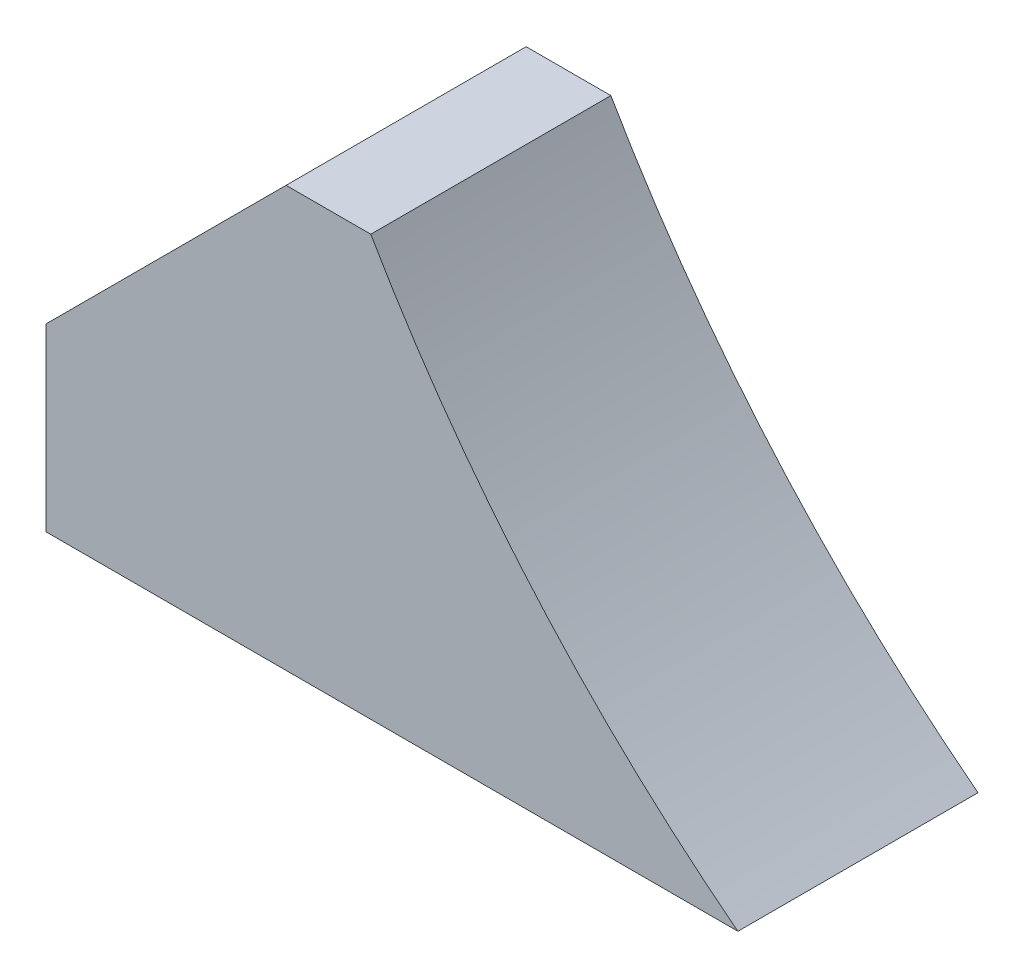
SolidWorks part; units mm, degrees
ref_plane "Front Plane" through (0, 0, 0) normal (0, 0, 1) x (1, 0, 0)
ref_plane "Top Plane" through (0, 0, 0) normal (0, 1, 0) x (1, 0, 0)
ref_plane "Right Plane" through (0, 0, 0) normal (1, 0, 0) x (0, 0, -1)
sketch "Sketch2" plane through (0, 0, 0) normal (0, 0, 1) x (1, 0, 0)
  line L0 (-28.3947, 6.35) -> (-101.6, 6.35)
  line L1 (-101.6, 6.35) -> (-101.6, 50.8)
  line L2 (-101.6, 50.8) -> (-67.2396, 50.8)
  line L3 (-67.2396, 50.8) -> (-101.6, 50.8) construction
  line L4 (-28.3666, 6.35) -> (-67.2396, 6.35) construction
  line L5 (-101.6, 50.8) -> (-101.6, 6.35) construction
  arc A0 (-28.3947, 6.35) -> (-67.2396, 50.8) centre (64.7583, 126.9548) cw
  circle A2 centre (64.7426, 127) radius 152.4 construction
extrude "Boss-Extrude1" add sketch "Sketch2" against normal blind 25.4
chamfer "Chamfer1" distance 25.4 angle 45 1 edges at (-101.6, 50.8, -12.7)
